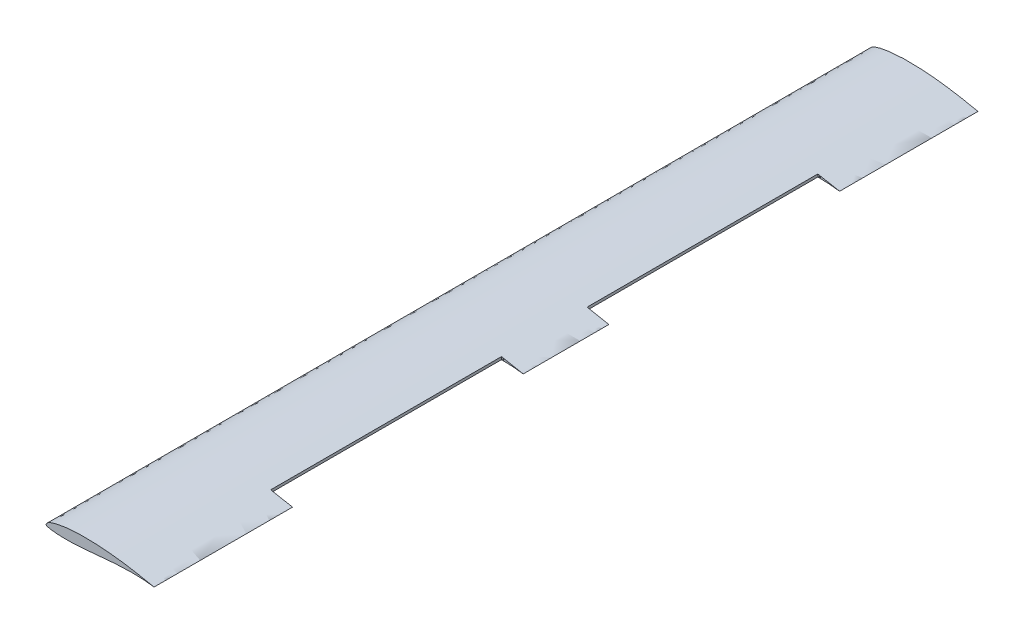
SolidWorks part; units mm, degrees
ref_plane "Front Plane" through (0, 0, 0) normal (0, 0, 1) x (1, 0, 0)
ref_plane "Top Plane" through (0, 0, 0) normal (0, 1, 0) x (1, 0, 0)
ref_plane "Right Plane" through (0, 0, 0) normal (1, 0, 0) x (0, 0, -1)
curve "Curve1"
  spline degree 3 poles (162.5054, 0.2399, 0) (164.3766, -0.0674, 0) (162.4984, 0.2974, 0) (160.9663, 0.6169, 0) (157.2301, 1.3585, 0) (152.6477, 2.2767, 0) (146.6748, 3.4526, 0) (139.6639, 4.7881, 0) (131.643, 6.2255, 0) (122.7797, 7.6781, 0) (113.2147, 9.0626, 0) (103.1148, 10.3087, 0) (92.6533, 11.3669, 0) (82.0087, 12.1836, 0) (71.3637, 12.7327, 0) (62.5731, 12.9388, 0) (55.6792, 12.9316, 0) (50.6638, 12.8397, 0) (45.7822, 12.6595, 0) (41.0552, 12.3904, 0) (36.5037, 12.0364, 0) (32.1469, 11.6018, 0) (28.0042, 11.0851, 0) (24.0917, 10.4983, 0) (20.4268, 9.8439, 0) (17.0258, 9.1308, 0) (13.9022, 8.3694, 0) (11.0683, 7.5656, 0) (8.5358, 6.7201, 0) (6.3124, 5.8329, 0) (4.4134, 4.8901, 0) (2.8451, 3.9032, 0) (1.6205, 2.9011, 0) (0.7312, 1.9381, 0) (0.1795, 1.0687, 0) (-0.0695, 0.2848, 0) (0.134, -0.4237, 0) (0.7641, -0.9032, 0) (1.6676, -1.285, 0) (2.8964, -1.6679, 0) (4.4544, -2.0608, 0) (6.3422, -2.4633, 0) (8.5547, -2.8492, 0) (11.0822, -3.197, 0) (13.9135, -3.4896, 0) (17.0355, -3.7334, 0) (20.4357, -3.9192, 0) (24.0994, -4.0549, 0) (28.0109, -4.1275, 0) (32.1529, -4.141, 0) (36.5088, -4.0825, 0) (41.0598, -3.9492, 0) (45.7863, -3.7367, 0) (50.6672, -3.4456, 0) (55.6815, -3.078, 0) (62.5754, -2.51, 0) (71.36, -1.6878, 0) (81.9977, -0.6546, 0) (92.6366, 0.3301, 0) (103.0952, 1.1742, 0) (113.1952, 1.8014, 0) (122.7632, 2.1758, 0) (131.6325, 2.2841, 0) (139.6597, 2.1473, 0) (146.6766, 1.8263, 0) (152.6515, 1.3776, 0) (157.2376, 0.925, 0) (160.9651, 0.442, 0) (162.5054, 0.2399, 0) (164.3766, -0.0674, 0) (162.4984, 0.2974, 0) knots -0.01889 -0.00847 -0.00213 0 0.002148 0.00855 0.019093 0.033602 0.051812 0.073403 0.097969 0.12507 0.15422 0.18491 0.21662 0.248811 0.280949 0.312507 0.327907 0.342969 0.357635 0.371852 0.385562 0.398705 0.41124 0.423118 0.434295 0.444729 0.454376 0.463215 0.471223 0.478387 0.484735 0.490273 0.49502 0.498937 0.502002 0.504262 0.5061 0.508218 0.511109 0.514949 0.519768 0.525568 0.532309 0.53997 0.548516 0.557914 0.568141 0.57915 0.590897 0.603335 0.616414 0.630088 0.644296 0.658978 0.674077 0.689528 0.721211 0.753454 0.785684 0.817334 0.84785 0.876721 0.903468 0.927655 0.94889 0.966808 0.98111 0.99153 0.99787 1 1.002148 1.00855 1.019093 periodic
sketch "Sketch2" plane through (0, 0, 0) normal (0, 0, 1) x (1, 0, 0)
  spline S0 degree 3 poles (162.5054, 0.2399) (164.3766, -0.0674) (162.4984, 0.2974) (160.9663, 0.6169) (157.2301, 1.3585) (152.6477, 2.2767) (146.6748, 3.4526) (139.6639, 4.7881) (131.643, 6.2255) (122.7797, 7.6781) (113.2147, 9.0626) (103.1148, 10.3087) (92.6533, 11.3669) (82.0087, 12.1836) (71.3637, 12.7327) (62.5731, 12.9388) (55.6792, 12.9316) (50.6638, 12.8397) (45.7822, 12.6595) (41.0552, 12.3904) (36.5037, 12.0364) (32.1469, 11.6018) (28.0042, 11.0851) (24.0917, 10.4983) (20.4268, 9.8439) (17.0258, 9.1308) (13.9022, 8.3694) (11.0683, 7.5656) (8.5358, 6.7201) (6.3124, 5.8329) (4.4134, 4.8901) (2.8451, 3.9032) (1.6205, 2.9011) (0.7312, 1.9381) (0.1795, 1.0687) (-0.0695, 0.2848) (0.134, -0.4237) (0.7641, -0.9032) (1.6676, -1.285) (2.8964, -1.6679) (4.4544, -2.0608) (6.3422, -2.4633) (8.5547, -2.8492) (11.0822, -3.197) (13.9135, -3.4896) (17.0355, -3.7334) (20.4357, -3.9192) (24.0994, -4.0549) (28.0109, -4.1275) (32.1529, -4.141) (36.5088, -4.0825) (41.0598, -3.9492) (45.7863, -3.7367) (50.6672, -3.4456) (55.6815, -3.078) (62.5754, -2.51) (71.36, -1.6878) (81.9977, -0.6546) (92.6366, 0.3301) (103.0952, 1.1742) (113.1952, 1.8014) (122.7632, 2.1758) (131.6325, 2.2841) (139.6597, 2.1473) (146.6766, 1.8263) (152.6515, 1.3776) (157.2376, 0.925) (160.9651, 0.442) (162.5054, 0.2399) (164.3766, -0.0674) (162.4984, 0.2974) knots -0.01889 -0.00847 -0.00213 0 0.002148 0.00855 0.019093 0.033602 0.051812 0.073403 0.097969 0.12507 0.15422 0.18491 0.21662 0.248811 0.280949 0.312507 0.327907 0.342969 0.357635 0.371852 0.385562 0.398705 0.41124 0.423118 0.434295 0.444729 0.454376 0.463215 0.471223 0.478387 0.484735 0.490273 0.49502 0.498937 0.502002 0.504262 0.5061 0.508218 0.511109 0.514949 0.519768 0.525568 0.532309 0.53997 0.548516 0.557914 0.568141 0.57915 0.590897 0.603335 0.616414 0.630088 0.644296 0.658978 0.674077 0.689528 0.721211 0.753454 0.785684 0.817334 0.84785 0.876721 0.903468 0.927655 0.94889 0.966808 0.98111 0.99153 0.99787 1 1.002148 1.00855 1.019093 only from (164, 0) to (164, 0) construction
  spline S1 degree 3 poles (162.5054, 0.2399) (164.3766, -0.0674) (162.4984, 0.2974) (160.9663, 0.6169) (157.2301, 1.3585) (152.6477, 2.2767) (146.6748, 3.4526) (139.6639, 4.7881) (131.643, 6.2255) (122.7797, 7.6781) (113.2147, 9.0626) (103.1148, 10.3087) (92.6533, 11.3669) (82.0087, 12.1836) (71.3637, 12.7327) (62.5731, 12.9388) (55.6792, 12.9316) (50.6638, 12.8397) (45.7822, 12.6595) (41.0552, 12.3904) (36.5037, 12.0364) (32.1469, 11.6018) (28.0042, 11.0851) (24.0917, 10.4983) (20.4268, 9.8439) (17.0258, 9.1308) (13.9022, 8.3694) (11.0683, 7.5656) (8.5358, 6.7201) (6.3124, 5.8329) (4.4134, 4.8901) (2.8451, 3.9032) (1.6205, 2.9011) (0.7312, 1.9381) (0.1795, 1.0687) (-0.0695, 0.2848) (0.134, -0.4237) (0.7641, -0.9032) (1.6676, -1.285) (2.8964, -1.6679) (4.4544, -2.0608) (6.3422, -2.4633) (8.5547, -2.8492) (11.0822, -3.197) (13.9135, -3.4896) (17.0355, -3.7334) (20.4357, -3.9192) (24.0994, -4.0549) (28.0109, -4.1275) (32.1529, -4.141) (36.5088, -4.0825) (41.0598, -3.9492) (45.7863, -3.7367) (50.6672, -3.4456) (55.6815, -3.078) (62.5754, -2.51) (71.36, -1.6878) (81.9977, -0.6546) (92.6366, 0.3301) (103.0952, 1.1742) (113.1952, 1.8014) (122.7632, 2.1758) (131.6325, 2.2841) (139.6597, 2.1473) (146.6766, 1.8263) (152.6515, 1.3776) (157.2376, 0.925) (160.9651, 0.442) (162.5054, 0.2399) (164.3766, -0.0674) (162.4984, 0.2974) knots -0.01889 -0.00847 -0.00213 0 0.002148 0.00855 0.019093 0.033602 0.051812 0.073403 0.097969 0.12507 0.15422 0.18491 0.21662 0.248811 0.280949 0.312507 0.327907 0.342969 0.357635 0.371852 0.385562 0.398705 0.41124 0.423118 0.434295 0.444729 0.454376 0.463215 0.471223 0.478387 0.484735 0.490273 0.49502 0.498937 0.502002 0.504262 0.5061 0.508218 0.511109 0.514949 0.519768 0.525568 0.532309 0.53997 0.548516 0.557914 0.568141 0.57915 0.590897 0.603335 0.616414 0.630088 0.644296 0.658978 0.674077 0.689528 0.721211 0.753454 0.785684 0.817334 0.84785 0.876721 0.903468 0.927655 0.94889 0.966808 0.98111 0.99153 0.99787 1 1.002148 1.00855 1.019093 only from (164, 0) to (164, 0)
extrude "Wing span" add sketch "Sketch2" along normal blind 1250
sketch "Sketch4" plane through (0, 0, 0) normal (0, 1, 0) x (1, 0, 0)
  line L0 (164, -1250) -> (164, 0) construction
  line L1 (164, -690) -> (131, -690)
  line L2 (164, -690) -> (164, -1040)
  line L3 (164, -1040) -> (131, -1040)
  line L4 (131, -690) -> (131, -1040)
  line L5 (-0.0003, -1250) -> (164, -1250) construction
  line L6 (164, -560) -> (131, -560)
  line L7 (164, -560) -> (164, -210)
  line L8 (164, -210) -> (131, -210)
  line L9 (131, -560) -> (131, -210)
  line L10 (164, 0) -> (-0.0003, 0) construction
  dimension "D1" = 33
  dimension "D2" = 350
  dimension "D3" = 33
  dimension "D4" = 350
  dimension "D5" = 210
  dimension "D6" = 210
extrude "Flap space" cut sketch "Sketch4" against normal blind 246 and the other way blind 110
sketch "Sketch5" plane through (0, 0, 560) normal (0, 0, -1) x (-1, 0, 0)
  line L1 (-131, 6.3137) -> (-131, 2.2433) construction
  circle A0 centre (-133.9389, 3.676) radius 1
  point P4 (-131, 4.2785)
  dimension "D1" = 2
  dimension "D2" = 3
extrude "Cut-Extrude3" cut sketch "Sketch5" against normal blind 29 and the other way blind 370
sketch "Sketch6" plane through (0, 0, 1040) normal (0, 0, -1) x (-1, 0, 0)
  line L1 (-131, 6.3137) -> (-131, 2.2433) construction
  circle A0 centre (-134, 4.2479) radius 1
  dimension "D1" = 2
  dimension "D2" = 3
extrude "Cut-Extrude4" cut sketch "Sketch6" against normal blind 22 and the other way blind 366
